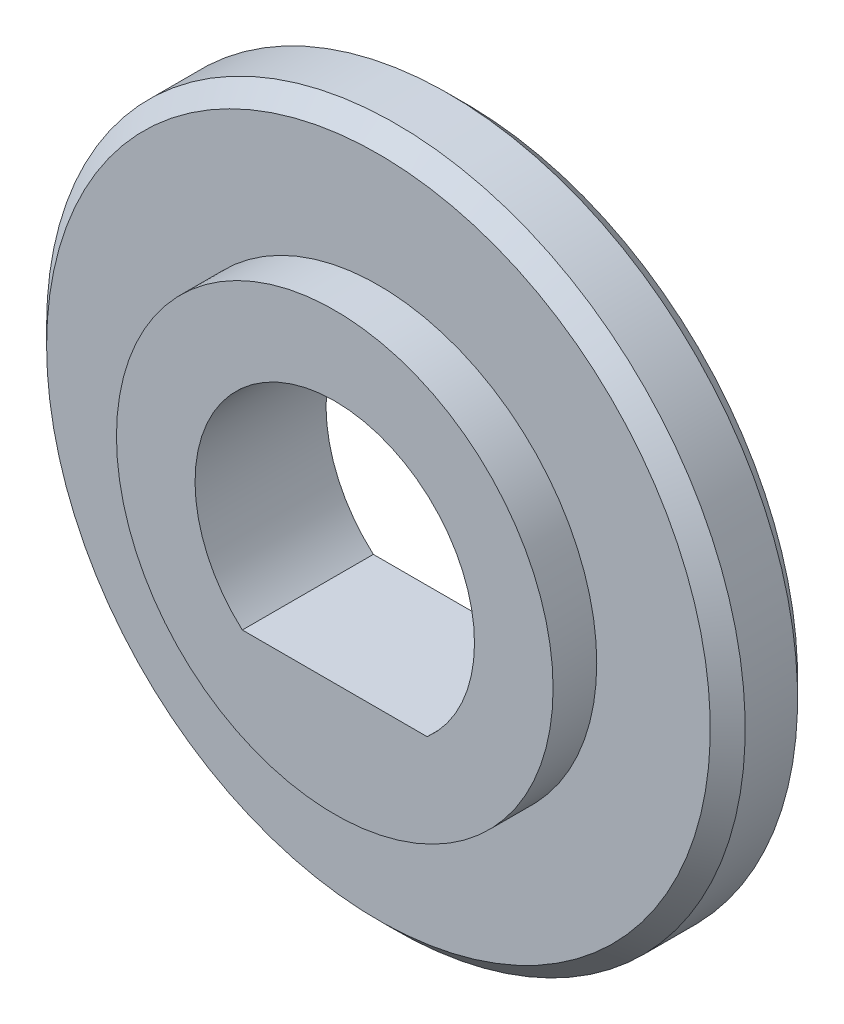
SolidWorks part; units mm, degrees
ref_plane "Front Plane" through (0, 0, 0) normal (0, 0, 1) x (1, 0, 0)
ref_plane "Top Plane" through (0, 0, 0) normal (0, 1, 0) x (1, 0, 0)
ref_plane "Right Plane" through (0, 0, 0) normal (1, 0, 0) x (0, 0, -1)
sketch "Sketch1" plane through (0, 0, 0) normal (0, 0, 1) x (1, 0, 0)
  circle A0 centre (0, 0) radius 12.5
  circle A1 centre (0, 0) radius 8
  dimension "D1" = 16
  dimension "D2" = 25
extrude "Boss-Extrude1" add sketch "Sketch1" along normal blind 2.5
ref_plane "Plane1" through (0, -6, 0) normal (0, 1, 0) x (-1, 0, 0)
sketch "Sketch3" plane through (0, 0, 0) normal (0, 0, -1) x (-1, 0, 0)
  circle A0 centre (0, 0) radius 8
  circle A1 centre (0, 0) radius 20
  dimension "D1" = 40
extrude "Boss-Extrude3" add sketch "Sketch3" along normal blind 5
chamfer "Chamfer2" distance 1 angle 45 2 edges at (-20, 0, 0) (-20, 0, -5)
sketch "Sketch4" plane through (0, -6, 0) normal (0, 1, 0) x (-1, 0, 0)
  line L0 (12.5, 2.5) -> (-12.5, 2.5) construction
  line L1 (5.5, 2.5) -> (-5.5, 2.5)
  line L2 (5.5, 2.5) -> (5.5, -5)
  line L3 (5.5, -5) -> (-5.5, -5)
  line L4 (-5.5, 2.5) -> (-5.5, -5)
  line L5 (-19, -5) -> (19, -5) construction
  dimension "D1" = 11
  dimension "D2" = 5.5
extrude "Boss-Extrude4" add sketch "Sketch4" against normal blind 3
